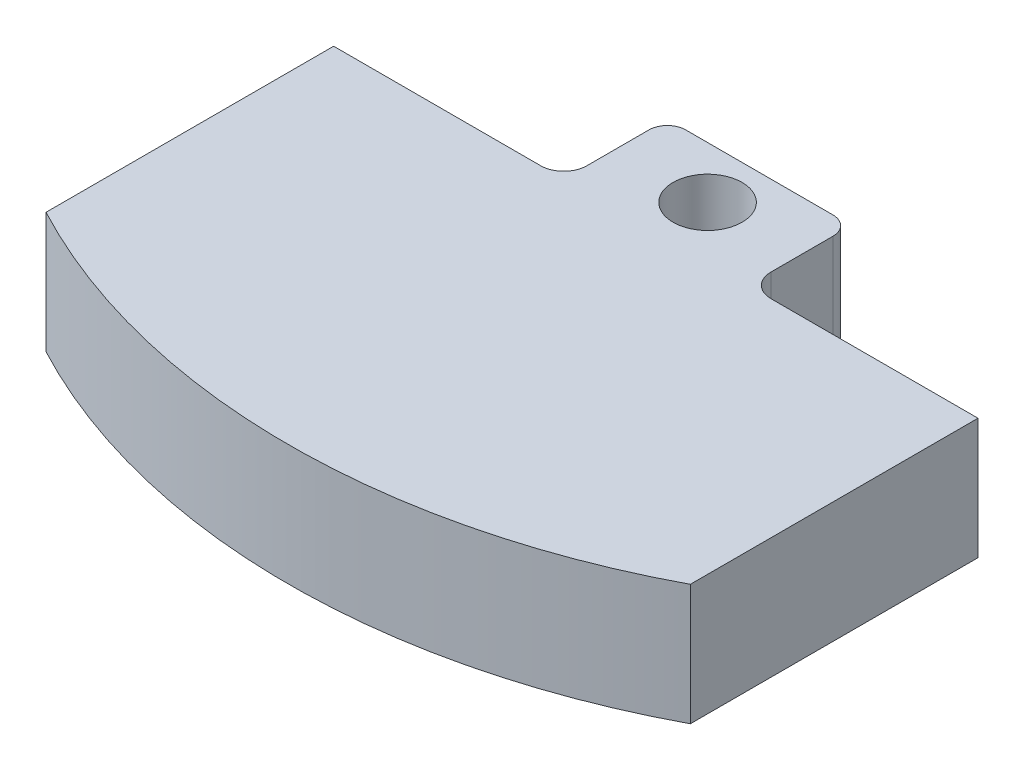
SolidWorks part; units mm, degrees
ref_plane "Front Plane" through (0, 0, 0) normal (0, 0, 1) x (1, 0, 0)
ref_plane "Top Plane" through (0, 0, 0) normal (0, 1, 0) x (1, 0, 0)
ref_plane "Right Plane" through (0, 0, 0) normal (1, 0, 0) x (0, 0, -1)
sketch "Sketch6" plane through (0, 0, 0) normal (0, 1, 0) x (1, 0, 0)
  line L1 (0, 0) -> (71.12, 0)
  line L2 (0, 0) -> (0, -43.18)
  line L4 (71.12, 0) -> (71.12, -43.18)
  arc A0 (71.12, -43.18) -> (0, -43.18) centre (35.56, 23.9876) cw
  dimension "D2" = 43.18
  dimension "D1" = 71.12
extrude "Boss-Extrude2" add sketch "Sketch6" along normal blind 13.335
sketch "Sketch10" plane through (0, 13.335, 0) normal (0, 1, 0) x (1, 0, 0)
  line L0 (35.56, 0) -> (35.56, -52.0124) construction
  line L1 (71.12, 0) -> (0, 0) construction
  line L2 (71.12, -11.43) -> (45.72, -11.43)
  line L3 (0, 0) -> (25.4, 0)
  line L4 (0, 0) -> (0, -11.43)
  line L5 (0, -11.43) -> (25.4, -11.43)
  line L6 (25.4, 0) -> (25.4, -11.43)
  line L7 (45.72, 0) -> (45.72, -11.43)
  line L8 (71.12, 0) -> (45.72, 0)
  line L9 (71.12, 0) -> (71.12, -11.43)
  arc A0 (0, -43.18) -> (71.12, -43.18) centre (35.56, 23.9876) ccw construction
  dimension "D1" = 25.4
  dimension "D2" = 11.43
extrude "Cut-Extrude1" cut sketch "Sketch10" against normal through all
fillet "Fillet1" radius 2.54 2 edges at (45.72, 6.6675, 11.43) (25.4, 6.6675, 11.43)
fillet "Fillet2" radius 2.032 2 edges at (45.72, 6.6675, 0) (25.4, 6.6675, 0)
sketch "Sketch11" plane through (0, 0, 0) normal (0, -1, 0) x (1, 0, 0)
  line L0 (35.56, 0) -> (35.56, 52.0124) construction
  line L1 (43.688, 0) -> (27.432, 0) construction
  arc A0 (71.12, 43.18) -> (0, 43.18) centre (35.56, -23.9876) ccw construction
  circle A3 centre (35.56, 5.7189) radius 3.81
  dimension "D1" = 7.62
extrude "Cut-Extrude2" cut sketch "Sketch11" against normal through all
